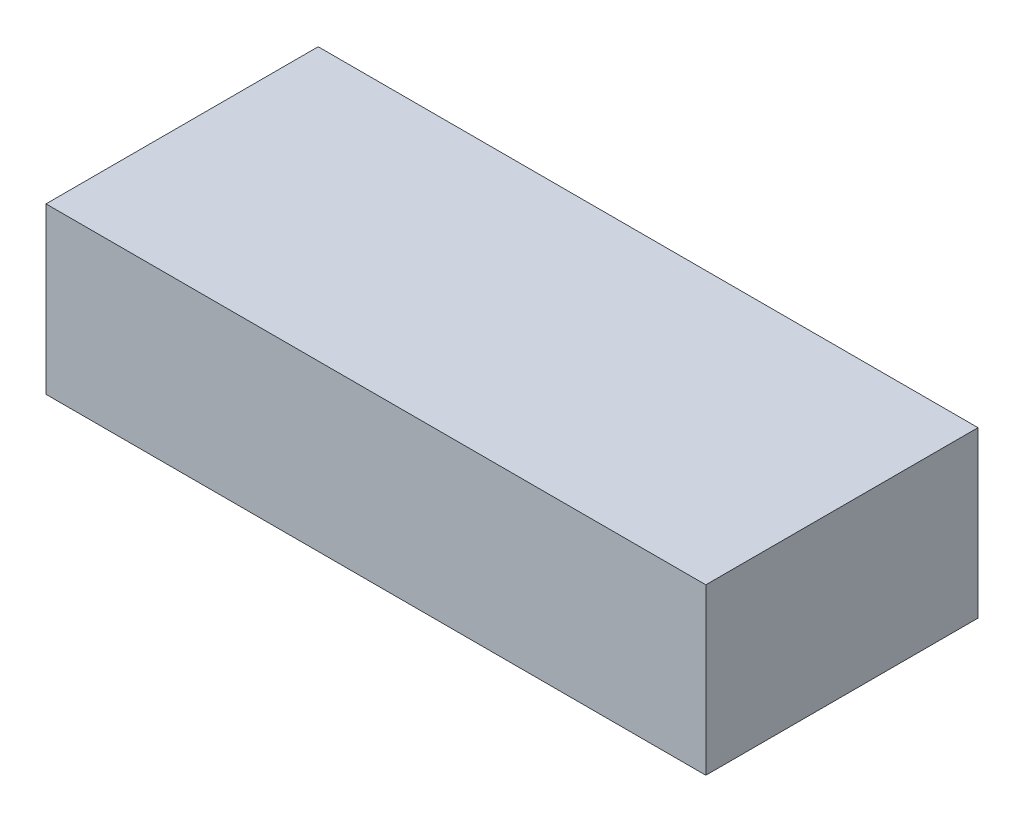
SolidWorks part; units mm, degrees
ref_plane "Front Plane" through (0, 0, 0) normal (0, 0, 1) x (1, 0, 0)
ref_plane "Top Plane" through (0, 0, 0) normal (0, 1, 0) x (1, 0, 0)
ref_plane "Right Plane" through (0, 0, 0) normal (1, 0, 0) x (0, 0, -1)
sketch "Sketch1" plane through (0, 0, 0) normal (0, 1, 0) x (1, 0, 0)
  line L1 (-47.1429, 16.5) -> (32.8571, 16.5)
  line L2 (-47.1429, 16.5) -> (-47.1429, -16.5)
  line L3 (-47.1429, -16.5) -> (32.8571, -16.5)
  line L4 (32.8571, 16.5) -> (32.8571, -16.5)
  dimension "D1" = 33
  dimension "D2" = 80
extrude "Boss-Extrude1" add sketch "Sketch1" along normal blind 20
